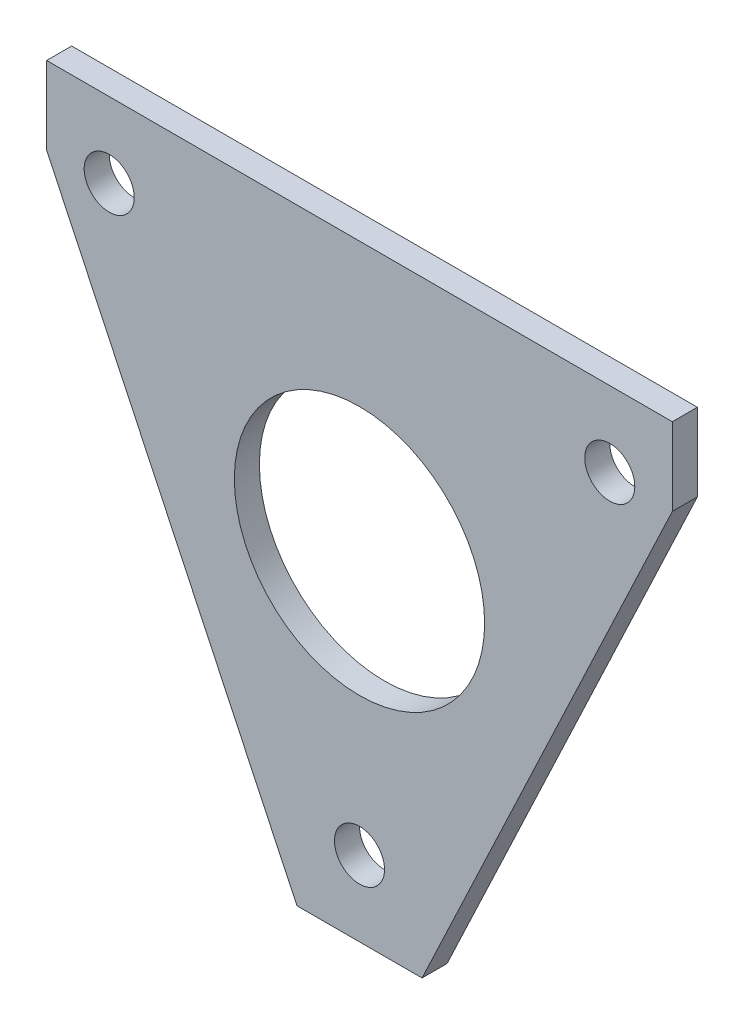
SolidWorks part; units mm, degrees
ref_plane "Front Plane" through (0, 0, 0) normal (0, 0, 1) x (1, 0, 0)
ref_plane "Top Plane" through (0, 0, 0) normal (0, 1, 0) x (1, 0, 0)
ref_plane "Right Plane" through (0, 0, 0) normal (1, 0, 0) x (0, 0, -1)
sketch "Sketch1" plane through (0, 0, 0) normal (0, 0, 1) x (1, 0, 0)
  line L0 (-71.425, 17.6855) -> (28.575, 17.6855)
  line L1 (28.575, 17.6855) -> (28.575, 5.2721)
  line L2 (-71.425, 17.6855) -> (-71.425, 5.2721)
  line L6 (-71.425, 5.2721) -> (-31.425, -79.3145)
  line L7 (28.575, 5.2721) -> (-11.425, -79.3145)
  line L8 (-31.425, -79.3145) -> (-11.425, -79.3145)
  circle A0 centre (-61.425, 5.6855) radius 4
  circle A1 centre (18.575, 5.6855) radius 4
  circle A2 centre (-21.425, -67.3145) radius 4
  point P3 (-21.425, -79.3145)
  point P17 (-31.425, -79.3145)
  point P20 (-11.425, -79.3145)
  dimension "D1" = 80
  dimension "D8" = 85
  dimension "D2" = 100
  dimension "D3" = 10
  dimension "D4" = 50
  dimension "D5" = 20
  dimension "D6" = 50
  dimension "D7" = 12
  dimension "D9" = 12
extrude "Boss-Extrude1" add sketch "Sketch1" along normal blind 4
sketch "Sketch2" plane through (0, 0, 4) normal (0, 0, 1) x (1, 0, 0)
  line L0 (-31.425, -79.3145) -> (-11.425, -79.3145) construction
  circle A0 centre (-21.425, -25.2125) radius 20
  point P0 (-21.425, -25.2125)
  dimension "D1" = 54.102
extrude "Cut-Extrude1" cut sketch "Sketch2" against normal blind 10
